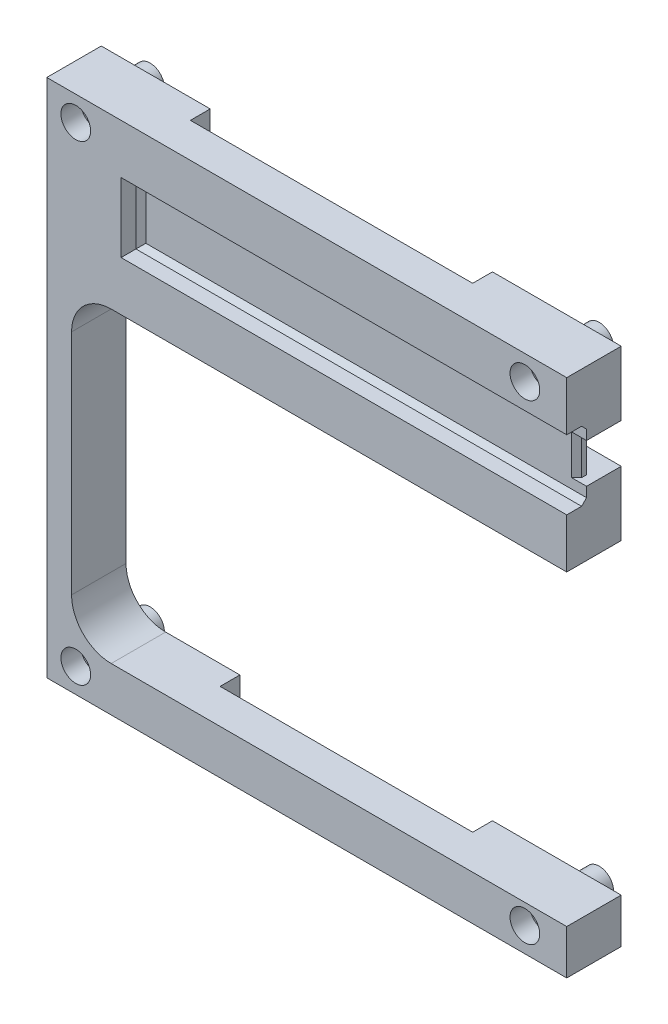
SolidWorks part; units mm, degrees
ref_plane "前视基准面" through (0, 0, 0) normal (0, 0, 1) x (1, 0, 0)
ref_plane "上视基准面" through (0, 0, 0) normal (0, 1, 0) x (1, 0, 0)
ref_plane "右视基准面" through (0, 0, 0) normal (1, 0, 0) x (0, 0, -1)
sketch "草图1" plane through (0, 0, 0) normal (0, 0, 1) x (1, 0, 0)
  line L1 (-52.5, 52.5) -> (52.5, 52.5)
  line L2 (52.5, 52.5) -> (52.5, -52.5)
  line L3 (-52.5, 52.5) -> (-52.5, -52.5)
  line L4 (-52.5, -52.5) -> (52.5, -52.5)
extrude "凸台-拉伸1" add sketch "草图1" along normal blind 15
sketch "草图2" plane through (0, 0, 15) normal (0, 0, 1) x (1, 0, 0)
  line L0 (8.25, 0) -> (-8.25, 0) construction
  circle A0 centre (-46.65, 47.555) radius 1.6
  circle A1 centre (44.05, 47.555) radius 1.6
  circle A2 centre (44.05, -47.555) radius 1.6
  circle A3 centre (-46.65, -47.555) radius 1.6
extrude "切除-拉伸1" cut sketch "草图2" against normal blind 15
sketch "草图3" plane through (0, 0, 15) normal (0, 0, 1) x (1, 0, 0)
  line L1 (52.5, -52.5) -> (52.5, 52.5) construction
  line L2 (52.5, -43.5) -> (-47.5, -43.5)
  line L3 (52.5, 18.5) -> (52.5, -43.5)
  line L4 (52.5, 18.5) -> (-47.5, 18.5)
  line L5 (-47.5, 18.5) -> (-47.5, -43.5)
extrude "切除-拉伸2" cut sketch "草图3" against normal blind 15
fillet "圆角1" radius 8 2 edges at (-47.5, -43.5, 7.5) (-47.5, 18.5, 7.5)
sketch "草图4" plane through (0, 0, 0) normal (0, 0, -1) x (-1, 0, 0)
  circle A0 centre (-44.05, -47.555) radius 2.9
  circle A1 centre (46.65, -47.555) radius 2.9
  circle A2 centre (-44.05, 47.555) radius 2.9
  circle A3 centre (46.65, 47.555) radius 2.9
extrude "切除-拉伸3" cut sketch "草图4" against normal blind 4 flip side to cut
sketch "草图5" plane through (0, 0, 4) normal (0, 0, -1) x (-1, 0, 0)
  line L1 (-52.5, -52.5) -> (52.5, -52.5) construction
  line L2 (24.5, -52.5) -> (24.5, -43.5)
  line L3 (39.5, -43.5) -> (-52.5, -43.5) construction
  line L5 (-26.5, -43.5) -> (-26.5, -52.5)
  line L6 (-26.5, -52.5) -> (24.5, -52.5)
  line L7 (-26.5, -43.5) -> (24.5, -43.5)
extrude "切除-拉伸4" cut sketch "草图5" against normal blind 4
sketch "草图6" plane through (0, 0, 4) normal (0, 0, -1) x (-1, 0, 0)
  line L1 (52.5, 52.5) -> (-52.5, 52.5) construction
  line L2 (-26.5, 52.5) -> (-26.5, 18.5)
  line L3 (-52.5, 18.5) -> (39.5, 18.5) construction
  line L5 (30.5, 52.5) -> (30.5, 18.5)
  line L6 (30.5, 18.5) -> (-26.5, 18.5)
  line L7 (-26.5, 52.5) -> (30.5, 52.5)
extrude "切除-拉伸5" cut sketch "草图6" against normal blind 4
sketch "草图7" plane through (0, 0, 4) normal (0, 0, -1) x (-1, 0, 0)
  line L0 (-26.5, 35.5) -> (-26.5, 39.5)
  line L2 (-26.5, 35.5) -> (-26.5, 31.5)
  line L3 (-26.5, 52.5) -> (-26.5, 18.5) construction
  line L4 (-26.5, 52.5) -> (-26.5, 18.5) construction
  line L5 (-26.5, 39.5) -> (-52.5, 39.5)
  line L6 (-52.5, 52.5) -> (-52.5, 18.5) construction
  line L7 (-52.5, 39.5) -> (-52.5, 31.5)
  line L8 (-52.5, 31.5) -> (-26.5, 31.5)
extrude "切除-拉伸6" cut sketch "草图7" against normal blind 4
fillet "圆角2" radius 4 2 edges at (26.5, 39.5, 6) (26.5, 31.5, 6)
sketch "草图8" plane through (0, 0, 15) normal (0, 0, 1) x (1, 0, 0)
  line L0 (-37.5, 42.5) -> (-37.5, 28.5)
  line L1 (52.5, 18.5) -> (52.5, 52.5) construction
  line L3 (-37.5, 42.5) -> (52.5, 42.5)
  line L5 (-37.5, 28.5) -> (52.5, 28.5)
  line L6 (52.5, 28.5) -> (52.5, 42.5)
extrude "切除-拉伸7" cut sketch "草图8" against normal blind 4
chamfer "倒角1" distance 1 angle 45 3 edges at (7.5, 28.5, 11) (7.5, 42.5, 11) (-37.5, 35.5, 11)
sketch "草图9" plane through (0, 0, 8) normal (0, 0, -1) x (-1, 0, 0)
  line L0 (-52.5, 39.5) -> (-50.5, 39.5)
  line L1 (-30.5, 39.5) -> (-52.5, 39.5) construction
  line L2 (-50.5, 39.5) -> (-50.5, 31.5)
  line L3 (-52.5, 31.5) -> (-30.5, 31.5) construction
  line L4 (-50.5, 31.5) -> (-52.5, 31.5)
  line L5 (-52.5, 31.5) -> (-52.5, 39.5)
extrude "切除-拉伸8" cut sketch "草图9" against normal blind 4
chamfer "倒角2" distance 1 angle 45 2 edges at (50.5, 35.5, 8) (50.5, 35.5, 11)
sketch "草图10" plane through (0, 0, 15) normal (0, 0, 1) x (1, 0, 0)
  circle A0 centre (-46.65, 47.555) radius 3
  circle A1 centre (44.05, 47.555) radius 3
  circle A2 centre (44.05, -47.555) radius 3
  circle A3 centre (-46.65, -47.555) radius 3
extrude "切除-拉伸9" cut sketch "草图10" against normal blind 4
sketch "草图11" plane through (0, 0, 4) normal (0, 0, -1) x (-1, 0, 0)
  line L42 (33.5, 49.5) -> (52.5, 49.5)
  line L43 (33.5, 18.5) -> (33.5, 49.5)
  line L44 (33.5, 49.5) -> (41.0798, 49.5)
  line L45 (33.5, 21.5) -> (33.5, 49.5)
  line L46 (49.5, -52.5) -> (49.5, 52.5)
  line L47 (49.5, 21.5) -> (49.5, 42.389)
  line L49 (33.5, 21.5) -> (49.5, 21.5)
  arc A19 (41.0798, 49.5) -> (49.5, 42.389) centre (46.65, 47.555) ccw
  dimension "D2" = 3
  dimension "D1" = 3
extrude "切除-拉伸10" cut sketch "草图11" against normal blind 5
fillet "圆角3" radius 2 5 edges at (-49.5, 31.9445, 9) (-41.5, 21.5, 9) (-33.5, 35.5, 9) (-37.2899, 49.5, 9) (-42.8432, 43.0474, 9)
